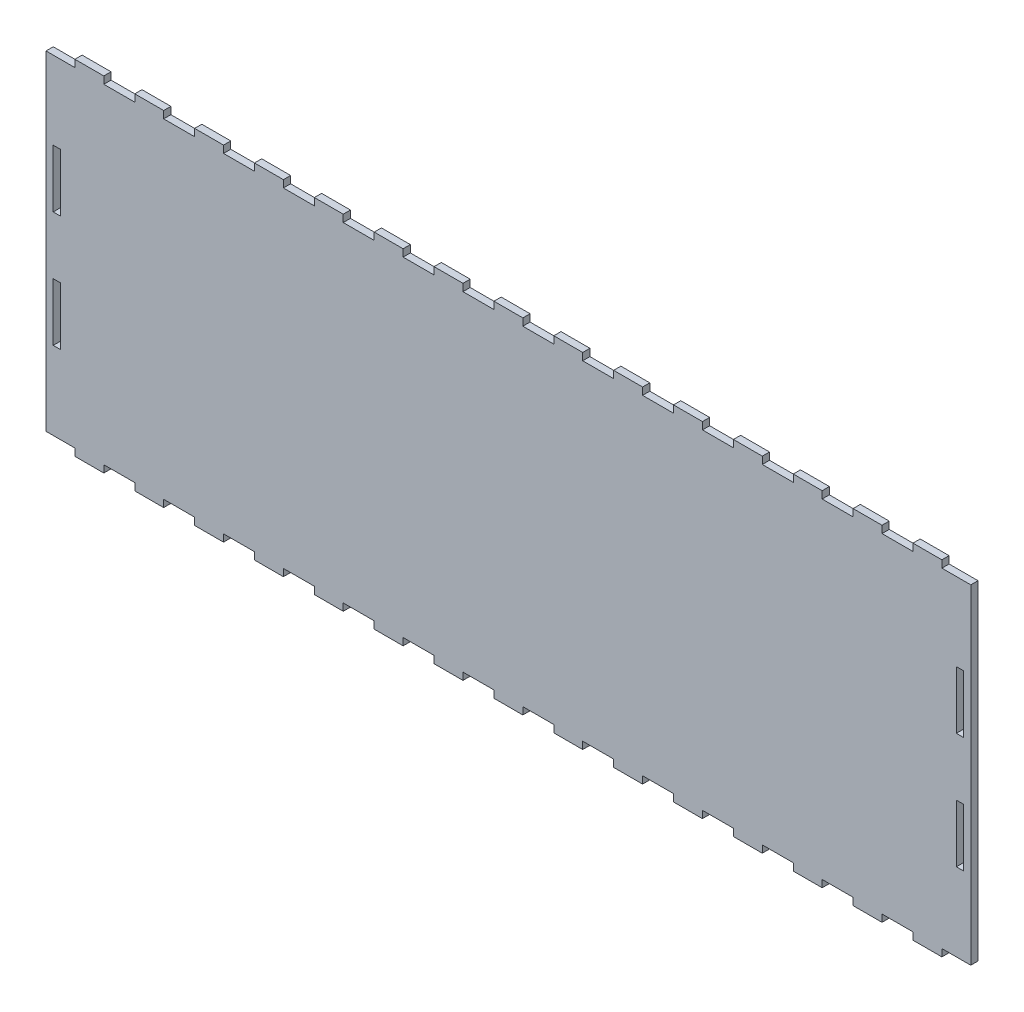
SolidWorks part; units mm, degrees
ref_plane "Front Plane" through (0, 0, 0) normal (0, 0, 1) x (1, 0, 0)
ref_plane "Top Plane" through (0, 0, 0) normal (0, 1, 0) x (1, 0, 0)
ref_plane "Right Plane" through (0, 0, 0) normal (1, 0, 0) x (0, 0, -1)
sketch "Sketch1" plane through (0, 0, 0) normal (0, 0, 1) x (1, 0, 0)
  line L8 (400.05, 110.49) -> (400.05, 85.09)
  line L9 (403.225, 110.49) -> (400.05, 110.49)
  line L10 (403.225, 85.09) -> (403.225, 110.49)
  line L11 (400.05, 85.09) -> (403.225, 85.09)
  line L16 (6.35, 34.29) -> (6.35, 59.69)
  line L17 (3.175, 34.29) -> (6.35, 34.29)
  line L18 (3.175, 59.69) -> (3.175, 34.29)
  line L19 (6.35, 59.69) -> (3.175, 59.69)
  line L24 (6.35, 85.09) -> (6.35, 110.49)
  line L25 (3.175, 85.09) -> (6.35, 85.09)
  line L26 (3.175, 110.49) -> (3.175, 85.09)
  line L27 (6.35, 110.49) -> (3.175, 110.49)
  line L32 (400.05, 59.69) -> (400.05, 34.29)
  line L33 (403.225, 59.69) -> (400.05, 59.69)
  line L34 (403.225, 34.29) -> (403.225, 59.69)
  line L35 (400.05, 34.29) -> (403.225, 34.29)
  line L280 (406.4, 0) -> (406.4, 144.78)
  line L281 (406.4, 144.78) -> (393.7, 144.78)
  line L282 (393.7, 144.78) -> (393.7, 147.955)
  line L283 (393.7, 147.955) -> (381, 147.955)
  line L284 (381, 147.955) -> (381, 144.78)
  line L285 (381, 144.78) -> (367.3929, 144.78)
  line L286 (367.3929, 144.78) -> (367.3929, 147.955)
  line L287 (367.3929, 147.955) -> (354.6929, 147.955)
  line L288 (354.6929, 147.955) -> (354.6929, 144.78)
  line L289 (354.6929, 144.78) -> (341.0857, 144.78)
  line L290 (341.0857, 144.78) -> (341.0857, 147.955)
  line L291 (341.0857, 147.955) -> (328.3857, 147.955)
  line L292 (328.3857, 147.955) -> (328.3857, 144.78)
  line L293 (328.3857, 144.78) -> (314.7786, 144.78)
  line L294 (314.7786, 144.78) -> (314.7786, 147.955)
  line L295 (314.7786, 147.955) -> (302.0786, 147.955)
  line L296 (302.0786, 147.955) -> (302.0786, 144.78)
  line L297 (302.0786, 144.78) -> (288.4714, 144.78)
  line L298 (288.4714, 144.78) -> (288.4714, 147.955)
  line L299 (288.4714, 147.955) -> (275.7714, 147.955)
  line L300 (275.7714, 147.955) -> (275.7714, 144.78)
  line L301 (275.7714, 144.78) -> (262.1643, 144.78)
  line L302 (262.1643, 144.78) -> (262.1643, 147.955)
  line L303 (262.1643, 147.955) -> (249.4643, 147.955)
  line L304 (249.4643, 147.955) -> (249.4643, 144.78)
  line L305 (249.4643, 144.78) -> (235.8571, 144.78)
  line L306 (235.8571, 144.78) -> (235.8571, 147.955)
  line L307 (235.8571, 147.955) -> (223.1571, 147.955)
  line L308 (223.1571, 147.955) -> (223.1571, 144.78)
  line L309 (223.1571, 144.78) -> (209.55, 144.78)
  line L310 (209.55, 144.78) -> (209.55, 147.955)
  line L311 (209.55, 147.955) -> (196.85, 147.955)
  line L312 (196.85, 147.955) -> (196.85, 144.78)
  line L313 (196.85, 144.78) -> (183.2429, 144.78)
  line L314 (183.2429, 144.78) -> (183.2429, 147.955)
  line L315 (183.2429, 147.955) -> (170.5429, 147.955)
  line L316 (170.5429, 147.955) -> (170.5429, 144.78)
  line L317 (170.5429, 144.78) -> (156.9357, 144.78)
  line L318 (156.9357, 144.78) -> (156.9357, 147.955)
  line L319 (156.9357, 147.955) -> (144.2357, 147.955)
  line L320 (144.2357, 147.955) -> (144.2357, 144.78)
  line L321 (144.2357, 144.78) -> (130.6286, 144.78)
  line L322 (130.6286, 144.78) -> (130.6286, 147.955)
  line L323 (130.6286, 147.955) -> (117.9286, 147.955)
  line L324 (117.9286, 147.955) -> (117.9286, 144.78)
  line L325 (117.9286, 144.78) -> (104.3214, 144.78)
  line L326 (104.3214, 144.78) -> (104.3214, 147.955)
  line L327 (104.3214, 147.955) -> (91.6214, 147.955)
  line L328 (91.6214, 147.955) -> (91.6214, 144.78)
  line L329 (91.6214, 144.78) -> (78.0143, 144.78)
  line L330 (78.0143, 144.78) -> (78.0143, 147.955)
  line L331 (78.0143, 147.955) -> (65.3143, 147.955)
  line L332 (65.3143, 147.955) -> (65.3143, 144.78)
  line L333 (65.3143, 144.78) -> (51.7071, 144.78)
  line L334 (51.7071, 144.78) -> (51.7071, 147.955)
  line L335 (51.7071, 147.955) -> (39.0071, 147.955)
  line L336 (39.0071, 147.955) -> (39.0071, 144.78)
  line L337 (39.0071, 144.78) -> (25.4, 144.78)
  line L338 (25.4, 144.78) -> (25.4, 147.955)
  line L339 (25.4, 147.955) -> (12.7, 147.955)
  line L340 (12.7, 147.955) -> (12.7, 144.78)
  line L341 (12.7, 144.78) -> (0, 144.78)
  line L342 (0, 144.78) -> (0, 0)
  line L343 (0, 0) -> (12.7, 0)
  line L344 (12.7, 0) -> (12.7, -3.175)
  line L345 (12.7, -3.175) -> (25.4, -3.175)
  line L346 (25.4, -3.175) -> (25.4, 0)
  line L347 (25.4, 0) -> (39.0071, 0)
  line L348 (39.0071, 0) -> (39.0071, -3.175)
  line L349 (39.0071, -3.175) -> (51.7071, -3.175)
  line L350 (51.7071, -3.175) -> (51.7071, 0)
  line L351 (51.7071, 0) -> (65.3143, 0)
  line L352 (65.3143, 0) -> (65.3143, -3.175)
  line L353 (65.3143, -3.175) -> (78.0143, -3.175)
  line L354 (78.0143, -3.175) -> (78.0143, 0)
  line L355 (78.0143, 0) -> (91.6214, 0)
  line L356 (91.6214, 0) -> (91.6214, -3.175)
  line L357 (91.6214, -3.175) -> (104.3214, -3.175)
  line L358 (104.3214, -3.175) -> (104.3214, 0)
  line L359 (104.3214, 0) -> (117.9286, 0)
  line L360 (117.9286, 0) -> (117.9286, -3.175)
  line L361 (117.9286, -3.175) -> (130.6286, -3.175)
  line L362 (130.6286, -3.175) -> (130.6286, 0)
  line L363 (130.6286, 0) -> (144.2357, 0)
  line L364 (144.2357, 0) -> (144.2357, -3.175)
  line L365 (144.2357, -3.175) -> (156.9357, -3.175)
  line L366 (156.9357, -3.175) -> (156.9357, 0)
  line L367 (156.9357, 0) -> (170.5429, 0)
  line L368 (170.5429, 0) -> (170.5429, -3.175)
  line L369 (170.5429, -3.175) -> (183.2429, -3.175)
  line L370 (183.2429, -3.175) -> (183.2429, 0)
  line L371 (183.2429, 0) -> (196.85, 0)
  line L372 (196.85, 0) -> (196.85, -3.175)
  line L373 (196.85, -3.175) -> (209.55, -3.175)
  line L374 (209.55, -3.175) -> (209.55, 0)
  line L375 (209.55, 0) -> (223.1571, 0)
  line L376 (223.1571, 0) -> (223.1571, -3.175)
  line L377 (223.1571, -3.175) -> (235.8571, -3.175)
  line L378 (235.8571, -3.175) -> (235.8571, 0)
  line L379 (235.8571, 0) -> (249.4643, 0)
  line L380 (249.4643, 0) -> (249.4643, -3.175)
  line L381 (249.4643, -3.175) -> (262.1643, -3.175)
  line L382 (262.1643, -3.175) -> (262.1643, 0)
  line L383 (262.1643, 0) -> (275.7714, 0)
  line L384 (275.7714, 0) -> (275.7714, -3.175)
  line L385 (275.7714, -3.175) -> (288.4714, -3.175)
  line L386 (288.4714, -3.175) -> (288.4714, 0)
  line L387 (288.4714, 0) -> (302.0786, 0)
  line L388 (302.0786, 0) -> (302.0786, -3.175)
  line L389 (302.0786, -3.175) -> (314.7786, -3.175)
  line L390 (314.7786, -3.175) -> (314.7786, 0)
  line L391 (314.7786, 0) -> (328.3857, 0)
  line L392 (328.3857, 0) -> (328.3857, -3.175)
  line L393 (328.3857, -3.175) -> (341.0857, -3.175)
  line L394 (341.0857, -3.175) -> (341.0857, 0)
  line L395 (341.0857, 0) -> (354.6929, 0)
  line L396 (354.6929, 0) -> (354.6929, -3.175)
  line L397 (354.6929, -3.175) -> (367.3929, -3.175)
  line L398 (367.3929, -3.175) -> (367.3929, 0)
  line L399 (367.3929, 0) -> (381, 0)
  line L400 (381, 0) -> (381, -3.175)
  line L401 (381, -3.175) -> (393.7, -3.175)
  line L402 (393.7, -3.175) -> (393.7, 0)
  line L403 (393.7, 0) -> (406.4, 0)
extrude "Boss-Extrude1" add sketch "Sketch1" along normal blind 3.175
